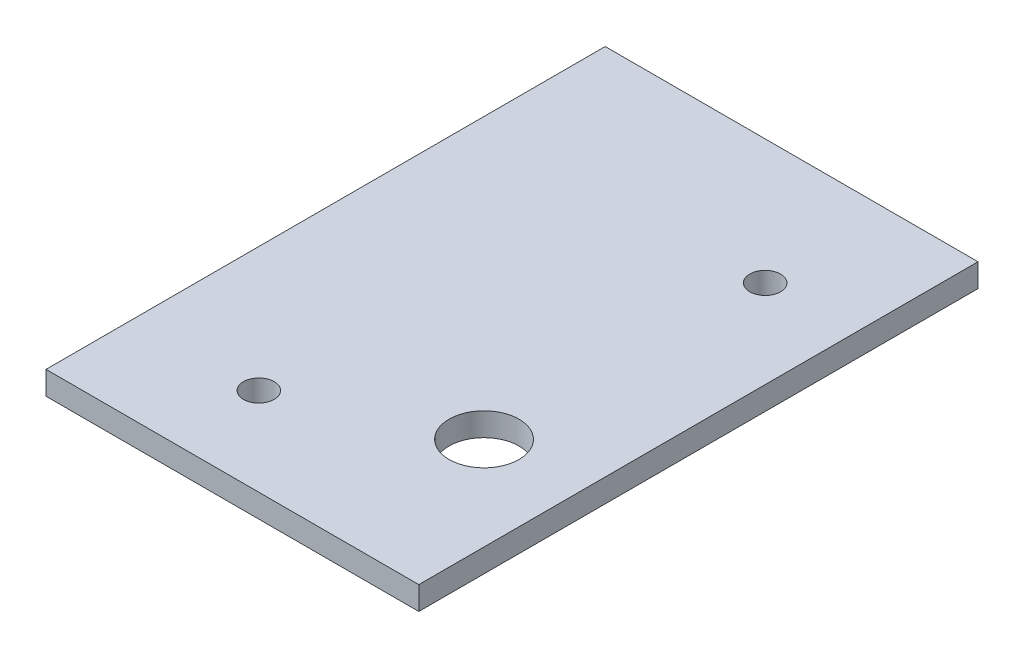
SolidWorks part; units mm, degrees
ref_plane "Front Plane" through (0, 0, 0) normal (0, 0, 1) x (1, 0, 0)
ref_plane "Top Plane" through (0, 0, 0) normal (0, 1, 0) x (1, 0, 0)
ref_plane "Right Plane" through (0, 0, 0) normal (1, 0, 0) x (0, 0, -1)
sketch "Sketch1" plane through (0, 0, 0) normal (0, 1, 0) x (1, 0, 0)
  line L1 (-25.4, 38.1) -> (25.4, 38.1)
  line L2 (-25.4, 38.1) -> (-25.4, -38.1)
  line L3 (-25.4, -38.1) -> (25.4, -38.1)
  line L4 (25.4, 38.1) -> (25.4, -38.1)
  line L5 (-25.4, 38.1) -> (25.4, -38.1) construction
  line L6 (-25.4, -38.1) -> (25.4, 38.1) construction
  point P4 (0, 0)
  dimension "D1" = 50.8
  dimension "D2" = 76.2
extrude "Boss-Extrude1" add sketch "Sketch1" along normal blind 3.175
sketch "Sketch2" plane through (0, 3.175, 0) normal (0, 1, 0) x (1, 0, 0)
  line L0 (12.7, 38.1) -> (12.7, -38.1) construction
  line L1 (25.4, 38.1) -> (-25.4, 38.1) construction
  line L2 (-25.4, -38.1) -> (25.4, -38.1) construction
  line L3 (-25.4, -16.51) -> (25.4, -16.51) construction
  line L4 (-25.4, 38.1) -> (-25.4, -38.1) construction
  line L5 (25.4, -38.1) -> (25.4, 38.1) construction
  circle A0 centre (12.7, -16.51) radius 4.7625
  dimension "D3" = 9.525
  dimension "D1" = 38.1
  dimension "D2" = 54.61
extrude "Cut-Extrude1" cut sketch "Sketch2" against normal through all
sketch "Sketch3" plane through (0, 3.175, 0) normal (0, 1, 0) x (1, 0, 0)
  circle A0 centre (13.4, 21.1) radius 2.1 construction
  circle A1 centre (13.4, 21.1) radius 2.1
  circle A2 centre (-8.4, -26.1) radius 2.1 construction
  circle A3 centre (-8.4, -26.1) radius 2.1
extrude "Cut-Extrude2" cut sketch "Sketch3" against normal through all
